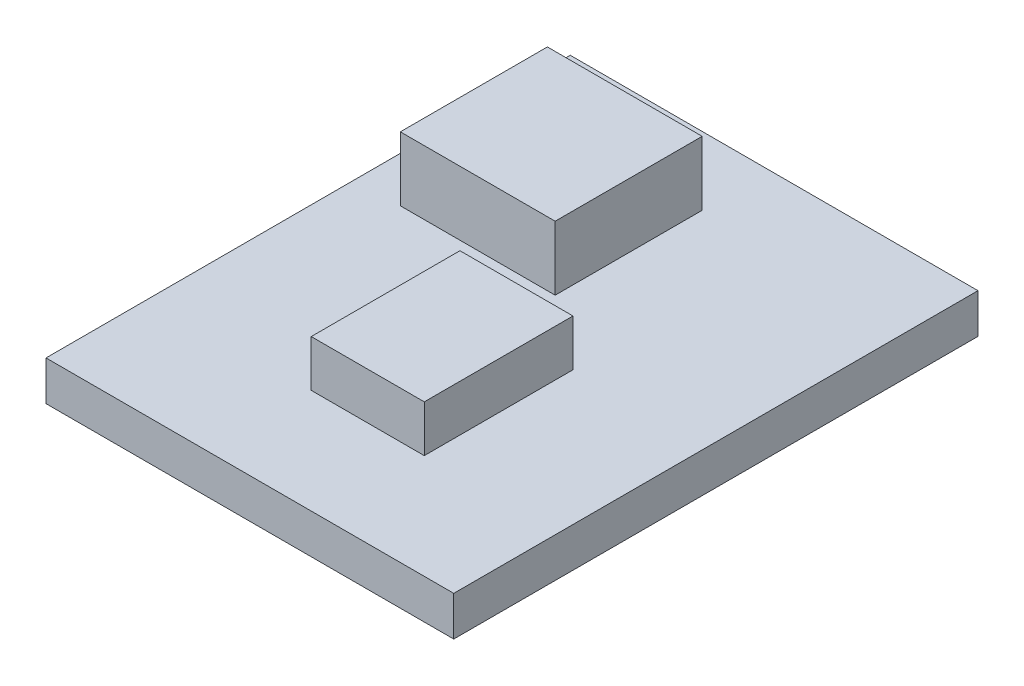
SolidWorks part; units mm, degrees
ref_plane "Front Plane" through (0, 0, 0) normal (0, 0, 1) x (1, 0, 0)
ref_plane "Top Plane" through (0, 0, 0) normal (0, 1, 0) x (1, 0, 0)
ref_plane "Right Plane" through (0, 0, 0) normal (1, 0, 0) x (0, 0, -1)
sketch "Sketch1" plane through (0, 0, 0) normal (0, 1, 0) x (1, 0, 0)
  line L1 (-7.746, 0) -> (9.754, 0)
  line L2 (-7.746, 0) -> (-7.746, -22.5)
  line L3 (-7.746, -22.5) -> (9.754, -22.5)
  line L4 (9.754, 0) -> (9.754, -22.5)
  dimension "D1" = 22.5
  dimension "D2" = 17.5
extrude "Boss-Extrude1" add sketch "Sketch1" along normal blind 1.7
sketch "Sketch2" plane through (0, 1.7, 0) normal (0, 1, 0) x (1, 0, 0)
  line L1 (-5.7964, -2.9318) -> (0.8486, -2.9318)
  line L2 (-5.7964, -2.9318) -> (-5.7964, -9.2422)
  line L3 (-5.7964, -9.2422) -> (0.8486, -9.2422)
  line L4 (0.8486, -2.9318) -> (0.8486, -9.2422)
extrude "Boss-Extrude2" add sketch "Sketch2" along normal blind 2.75
sketch "Sketch3" plane through (0, 1.7, 0) normal (0, 1, 0) x (1, 0, 0)
  line L1 (-0.8485, -11.6324) -> (4.0038, -11.6324)
  line L2 (-0.8485, -11.6324) -> (-0.8485, -18.0145)
  line L3 (-0.8485, -18.0145) -> (4.0038, -18.0145)
  line L4 (4.0038, -11.6324) -> (4.0038, -18.0145)
extrude "Boss-Extrude3" add sketch "Sketch3" along normal blind 2
